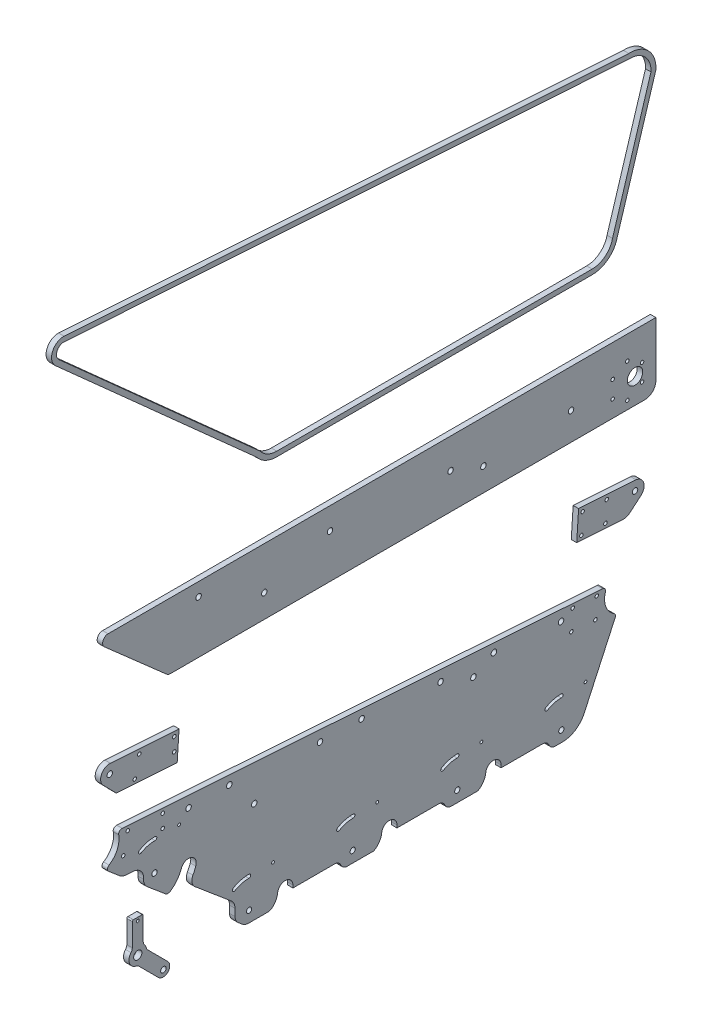
SolidWorks part; units mm, degrees
ref_plane "前视基准面" through (0, 0, 0) normal (0, 0, 1) x (1, 0, 0)
ref_plane "上视基准面" through (0, 0, 0) normal (0, 1, 0) x (1, 0, 0)
ref_plane "右视基准面" through (0, 0, 0) normal (1, 0, 0) x (0, 0, -1)
sketch "草图1" plane through (0, 0, 0) normal (1, 0, 0) x (0, 0, -1)
  line L14 (-230.0465, 110.9643) -> (-222.0465, 110.9643)
  line L15 (-216.9793, 80.6181) -> (-198.5946, 62.2334)
  line L16 (-221.0465, 89.2709) -> (-221.0465, 109.9643)
  line L17 (-231.0465, 89.2709) -> (-231.0465, 109.9643)
  line L18 (-225.09, 71.7583) -> (-207.0798, 53.7481)
  line L19 (105.5834, 65.6055) -> (105.5834, 63.2056)
  line L20 (10.5834, 65.6055) -> (10.5834, 63.181)
  line L21 (-236.8297, 149.6899) -> (-229.9878, 149.2348)
  line L22 (-84.4166, 65.6055) -> (-84.4166, 63.2014)
  line L23 (-137.2631, 67.0436) -> (-137.2631, 73.5793)
  line L24 (-252.6112, 160.4369) -> (-242.6047, 152.0164)
  line L25 (-200.3246, 116.3858) -> (-217.1392, 130.5351)
  line L26 (-173.8485, 109.0202) -> (-140.8245, 81.2308)
  line L27 (105.5834, 63.2056) -> (143.6903, 63.2056)
  line L28 (10.5834, 63.181) -> (48.7171, 63.181)
  line L29 (-84.4166, 63.2014) -> (-46.2562, 63.2014)
  line L30 (154.9968, 55.6055) -> (161.4882, 55.6055)
  line L31 (60.0128, 55.6055) -> (84.3359, 55.6055)
  line L32 (-34.8893, 55.6055) -> (-10.6641, 55.6055)
  line L33 (-240.2719, 188.3412) -> (198.1907, 158.5594)
  line L34 (181.4745, 68.4105) -> (209.7419, 129.8528)
  line L35 (-130.8865, 57.9541) -> (-134.414, 60.9224)
  line L36 (-124.4479, 55.6055) -> (-107.3213, 55.6055)
  line L37 (-190.0505, 215.1099) -> (-188.328, 241.0072)
  line L38 (-188.328, 241.0072) -> (-251.0362, 245.1782)
  line L39 (-245.6413, 218.8075) -> (-257.5624, 231.0237)
  line L40 (-245.6413, 218.8075) -> (-190.0505, 215.1099)
  line L47 (174.6512, 206.6476) -> (216.2373, 203.8816)
  line L48 (223.3686, 206.2326) -> (233.4205, 214.7564)
  line L49 (176.39, 232.7899) -> (174.6512, 206.6476)
  line L50 (176.39, 232.7899) -> (228.7265, 229.3088)
  line L122 (-293.5152, 599.4283) -> (222.2511, 565.1227)
  line L131 (242.4299, 544.9439) -> (207.3442, 430.9372)
  line L133 (188.77, 415.937) -> (-99.1762, 415.937)
  line L150 (-114.4994, 423.7032) -> (-297.9902, 587.7064)
  line L160 (246.8783, 348.5788) -> (246.8783, 298.5788)
  line L161 (246.8783, 348.5788) -> (-253.1217, 348.5788)
  line L162 (-256.4251, 339.8255) -> (-199.8991, 290.0748)
  line L164 (236.8783, 288.5788) -> (-195.935, 288.5788)
  line L166 (-293.3467, 603.927) -> (222.2719, 569.6313)
  line L167 (246.8783, 544.0995) -> (211.6993, 429.7897)
  line L168 (188.77, 411.437) -> (-99.1762, 411.437)
  line L169 (-117.831, 420.6454) -> (-300.9891, 584.3512)
  circle A0 centre (-228.79, 221.5342) radius 1.6
  arc A1 (-251.0362, 245.1782) -> (-257.5624, 231.0237) centre (-251.59, 236.8518) ccw
  circle A2 centre (-224.6325, 239.25) radius 1.6
  circle A3 centre (-251.59, 236.8518) radius 2.5
  circle A4 centre (-170.5361, 336.4269) radius 2.5
  circle A5 centre (89.4639, 309.8122) radius 2.5
  circle A6 centre (-192.7061, 237.0812) radius 1.6
  circle A7 centre (59.4639, 321.1287) radius 2.5
  circle A8 centre (-192.79, 225.0815) radius 1.6
  circle A11 centre (-110.5361, 309.8122) radius 2.5
  circle A12 centre (227.8783, 311.5857) radius 7
  circle A13 centre (169.4639, 313.8122) radius 2.5
  circle A14 centre (-50.5361, 328.4452) radius 2.5
  arc A15 (246.8783, 298.5788) -> (236.8783, 288.5788) centre (236.8783, 298.5788) cw
  circle A28 centre (234.3017, 319.3357) radius 1.6
  circle A29 centre (220.8783, 327.0857) radius 1.6
  circle A30 centre (207.4549, 319.3357) radius 1.6
  circle A31 centre (207.4549, 303.8357) radius 1.6
  circle A32 centre (220.8783, 296.0857) radius 1.6
  circle A33 centre (234.3017, 303.8357) radius 1.6
  arc A59 (-232.2003, 86.0761) -> (-227.6336, 73.1233) centre (-226.0465, 80.9643) ccw
  arc A60 (-218.291, 82.927) -> (-219.8926, 86.0761) centre (-226.0465, 80.9643) ccw
  arc A61 (-198.5946, 62.2334) -> (-207.0798, 53.7481) centre (-202.8372, 57.9907) cw
  circle A62 centre (-226.0465, 80.9643) radius 3.75
  arc A63 (-225.09, 71.7583) -> (-227.6336, 73.1233) centre (-228.6255, 68.2227) ccw
  arc A64 (-231.0465, 89.2709) -> (-232.2003, 86.0761) centre (-236.0465, 89.2709) cw
  arc A65 (-216.9793, 80.6181) -> (-218.291, 82.927) centre (-213.4438, 84.1537) cw
  arc A66 (-221.0465, 89.2709) -> (-219.8926, 86.0761) centre (-216.0465, 89.2709) ccw
  arc A67 (-221.0465, 109.9643) -> (-222.0465, 110.9643) centre (-222.0465, 109.9643) ccw
  arc A68 (-231.0465, 109.9643) -> (-230.0465, 110.9643) centre (-230.0465, 109.9643) cw
  circle A69 centre (-226.0465, 107.9643) radius 1.3
  circle A70 centre (-202.5944, 57.7479) radius 2.5
  circle A71 centre (160.3391, 151.5407) radius 2.5
  circle A72 centre (-179.6609, 174.1553) radius 2.5
  circle A73 centre (192.9424, 155.3853) radius 1.6
  circle A74 centre (50.3391, 158.8572) radius 2.5
  arc A75 (-130.8865, 57.9541) -> (-124.4479, 55.6055) centre (-124.4479, 65.6055) ccw
  arc A76 (161.4882, 55.6055) -> (181.4745, 68.4105) centre (161.4882, 77.6055) ccw
  circle A77 centre (80.3391, 147.5407) radius 2.5
  arc A78 (-40.9159, 59.9364) -> (-39.59, 57.8768) centre (-29.8465, 65.6055) ccw
  circle A79 centre (-119.6609, 147.5407) radius 2.5
  circle A80 centre (170.9909, 156.8454) radius 1.6
  circle A81 centre (-59.6609, 166.1737) radius 2.5
  arc A82 (54.0884, 59.8547) -> (55.122, 58.1299) centre (65.6415, 65.6055) ccw
  arc A83 (149.0664, 59.8697) -> (150.1013, 58.1364) centre (160.6415, 65.6055) ccw
  arc A84 (149.0664, 59.8697) -> (143.6903, 63.2056) centre (143.6903, 57.2056) ccw
  arc A85 (48.7171, 63.181) -> (54.0884, 59.8547) centre (48.7171, 57.181) cw
  arc A86 (-46.2562, 63.2014) -> (-40.9159, 59.9364) centre (-46.2562, 57.2014) cw
  circle A87 centre (169.783, 138.6855) radius 1.6
  circle A88 centre (191.7345, 137.2255) radius 1.6
  circle A89 centre (-235.1682, 183.9052) radius 1.6
  circle A90 centre (-203.2418, 181.7363) radius 1.6
  circle A91 centre (-239.3257, 166.1893) radius 1.6
  arc A92 (-103.7076, 56.8158) -> (-107.3213, 55.6055) centre (-107.3213, 61.6055) cw
  arc A93 (60.0128, 55.6055) -> (55.122, 58.1299) centre (60.0128, 61.6055) cw
  circle A94 centre (-188.2832, 165.2455) radius 1.3
  arc A95 (-34.8893, 55.6055) -> (-39.59, 57.8768) centre (-34.8893, 61.6055) cw
  arc A96 (-179.6609, 127.2391) -> (-193.1471, 110.3459) centre (-210.7713, 138.2455) cw construction
  arc A97 (-173.8485, 109.0202) -> (-175.7099, 118.992) centre (-168.6976, 115.1413) cw
  arc A98 (-196.8856, 116.264) -> (-200.3246, 116.3858) centre (-198.4616, 120.3771) cw
  arc A99 (-196.8856, 116.264) -> (-186.2601, 129.5738) centre (-210.7713, 138.2455) ccw
  arc A100 (154.9968, 55.6055) -> (150.1013, 58.1364) centre (154.9968, 61.6055) cw
  arc A101 (-140.8245, 81.2308) -> (-137.2631, 73.5793) centre (-147.2631, 73.5793) cw
  arc A102 (-236.8297, 149.6899) -> (-242.6047, 152.0164) centre (-236.1661, 159.6678) cw
  arc A103 (-229.9878, 149.2348) -> (-220.7032, 138.241) centre (-230.6515, 139.2569) cw
  arc A104 (-220.7032, 138.241) -> (-217.1392, 130.5351) centre (-211.8741, 137.6474) ccw
  arc A105 (-137.2631, 67.0436) -> (-134.414, 60.9224) centre (-129.2631, 67.0436) ccw
  arc A106 (-173.0617, 124.9044) -> (-186.2601, 129.5738) centre (-179.6609, 127.2391) ccw
  arc A107 (-175.7099, 118.992) -> (-173.0617, 124.9044) centre (-210.7713, 138.2455) ccw
  arc A108 (209.7419, 129.8528) -> (208.6362, 133.6318) centre (207.0165, 131.1066) ccw
  arc A109 (198.1907, 158.5594) -> (200.8593, 154.6992) centre (197.9874, 155.5663) cw
  arc A110 (-252.6112, 160.4369) -> (-252.2413, 165.2938) centre (-250.6796, 162.7323) cw
  arc A111 (-240.2719, 188.3412) -> (-243.4291, 184.8241) centre (-240.4752, 185.3481) ccw
  arc A112 (-210.2832, 165.2455) -> (-223.8045, 161.6159) centre (-210.7713, 140.0637) ccw construction
  arc A113 (-210.2522, 166.8452) -> (-224.6325, 162.985) centre (-210.7713, 140.0637) ccw
  arc A114 (-210.3142, 163.6458) -> (-222.9766, 160.2468) centre (-210.7713, 140.0637) ccw
  arc A115 (-210.3142, 163.6458) -> (-210.2522, 166.8452) centre (-210.2832, 165.2455) ccw
  arc A116 (-224.6325, 162.985) -> (-222.9766, 160.2468) centre (-223.8045, 161.6159) ccw
  circle A117 centre (-203.3257, 169.7366) radius 1.6
  circle A118 centre (-210.7713, 138.2455) radius 2.4
  circle A119 centre (-102.5698, 92.6055) radius 1.3
  arc A120 (-100.2131, 60.9055) -> (-103.7076, 56.8158) centre (-111.2189, 66.7716) cw
  circle A121 centre (87.6415, 92.6055) radius 1.3
  circle A122 centre (65.6415, 65.6055) radius 2.4
  arc A123 (89.7869, 60.9055) -> (91.5834, 65.6055) centre (79.7252, 67.4448) ccw
  circle A124 centre (-21.7236, 165.6547) radius 2.5
  arc A125 (-84.4166, 65.6055) -> (-98.4166, 65.6055) centre (-91.4166, 65.6055) ccw
  arc A126 (-5.2131, 60.9055) -> (-3.4166, 65.6055) centre (-15.2748, 67.4448) ccw
  circle A127 centre (-29.8465, 65.6055) radius 2.4
  circle A128 centre (-7.3585, 92.6055) radius 1.3
  arc A129 (-5.2131, 60.9055) -> (-10.6641, 55.6055) centre (-16.2189, 66.7716) cw
  circle A130 centre (-142.4886, 173.6873) radius 2.5
  circle A131 centre (99.0415, 157.6222) radius 2.5
  arc A134 (89.7869, 60.9055) -> (84.3359, 55.6055) centre (78.7811, 66.7716) cw
  arc A135 (105.5834, 65.6055) -> (91.5834, 65.6055) centre (98.5834, 65.6055) ccw
  arc A136 (-100.2131, 60.9055) -> (-98.4166, 65.6055) centre (-110.2748, 67.4448) ccw
  circle A137 centre (182.6415, 92.6055) radius 1.3
  arc A139 (-91.4166, 65.6055) -> (-95.4814, 55.6055) centre (-110.2748, 67.4448) cw construction
  circle A142 centre (-124.4166, 65.6055) radius 2.4
  arc A143 (-252.2413, 165.2938) -> (-243.4291, 184.8241) centre (-262.1257, 181.5069) ccw
  circle A145 centre (160.6415, 65.6055) radius 2.4
  arc A146 (200.8593, 154.6992) -> (208.6362, 133.6318) centre (218.6954, 149.3142) ccw
  arc A147 (10.5834, 65.6055) -> (-3.4166, 65.6055) centre (3.5834, 65.6055) ccw
  arc A148 (-29.3585, 92.6055) -> (-42.8798, 88.9759) centre (-29.8465, 67.4237) ccw construction
  arc A149 (-29.3275, 94.2052) -> (-43.7077, 90.345) centre (-29.8465, 67.4237) ccw
  arc A151 (-29.3895, 91.0058) -> (-42.0518, 87.6068) centre (-29.8465, 67.4237) ccw
  arc A152 (-29.3895, 91.0058) -> (-29.3275, 94.2052) centre (-29.3585, 92.6055) ccw
  arc A153 (-43.7077, 90.345) -> (-42.0518, 87.6068) centre (-42.8798, 88.9759) ccw
  arc A154 (-124.5698, 92.6055) -> (-138.0911, 88.9759) centre (-125.0579, 67.4237) ccw construction
  arc A155 (-124.5388, 94.2052) -> (-138.919, 90.345) centre (-125.0579, 67.4237) ccw
  arc A158 (-124.6008, 91.0058) -> (-137.2631, 87.6068) centre (-125.0579, 67.4237) ccw
  arc A159 (-124.6008, 91.0058) -> (-124.5388, 94.2052) centre (-124.5698, 92.6055) ccw
  arc A160 (-138.919, 90.345) -> (-137.2631, 87.6068) centre (-138.0911, 88.9759) ccw
  arc A161 (65.6415, 92.6055) -> (52.1202, 88.9759) centre (65.1535, 67.4237) ccw construction
  arc A163 (65.6725, 94.2052) -> (51.2923, 90.345) centre (65.1535, 67.4237) ccw
  arc A164 (65.6105, 91.0058) -> (52.9482, 87.6068) centre (65.1535, 67.4237) ccw
  arc A165 (65.6105, 91.0058) -> (65.6725, 94.2052) centre (65.6415, 92.6055) ccw
  circle A166 centre (180.1157, 228.5332) radius 1.6
  arc A169 (233.4205, 214.7564) -> (228.7265, 229.3088) centre (227.8783, 221.002) ccw
  circle A170 centre (200.8593, 208.9133) radius 1.6
  circle A171 centre (202.0672, 227.0732) radius 1.6
  circle A172 centre (227.8783, 221.002) radius 2.5
  circle A175 centre (178.9078, 210.3734) radius 1.6
  arc A176 (216.2373, 203.8816) -> (223.3686, 206.2326) centre (216.901, 213.8595) ccw
  arc A177 (51.2923, 90.345) -> (52.9482, 87.6068) centre (52.1202, 88.9759) ccw
  arc A178 (160.6415, 92.6055) -> (147.1202, 88.9759) centre (160.1535, 67.4237) ccw construction
  arc A180 (160.6725, 94.2052) -> (146.2923, 90.345) centre (160.1535, 67.4237) ccw
  arc A181 (160.6105, 91.0058) -> (147.9482, 87.6068) centre (160.1535, 67.4237) ccw
  arc A182 (160.6105, 91.0058) -> (160.6725, 94.2052) centre (160.6415, 92.6055) ccw
  arc A183 (146.2923, 90.345) -> (147.9482, 87.6068) centre (147.1202, 88.9759) ccw
  arc A481 (188.77, 415.937) -> (207.3442, 430.9372) centre (188.77, 434.937) ccw
  arc A521 (-199.8991, 290.0748) -> (-195.935, 288.5788) centre (-195.935, 294.5788) ccw
  arc A525 (-253.1217, 348.5788) -> (-256.4251, 339.8255) centre (-253.1217, 343.5788) ccw
  arc A526 (-293.5152, 599.4283) -> (-297.9902, 587.7064) centre (-293.5152, 592.7131) ccw
  arc A527 (-114.4994, 423.7032) -> (-99.1762, 415.937) centre (-99.1762, 434.937) ccw
  arc A528 (222.2511, 565.1227) -> (242.4299, 544.9439) centre (223.469, 546.1618) cw
  arc A529 (222.2719, 569.6313) -> (246.8783, 544.0995) centre (223.469, 546.1618) cw
  arc A530 (188.77, 411.437) -> (211.6993, 429.7897) centre (188.77, 434.937) ccw
  arc A531 (-117.831, 420.6454) -> (-99.1762, 411.437) centre (-99.1762, 434.937) ccw
  arc A532 (-293.3467, 603.927) -> (-300.9891, 584.3512) centre (-293.5152, 592.7131) ccw
  point P0 (-150, 0)
  point P1 (135, 0)
  point P9 (-344.9533, 138.7825)
  point P10 (187.1329, 101.1747)
  point P11 (165.9429, -19)
  point P12 (-156.9154, -19)
  point P90 (-202.4626, 49.1308)
  point P124 (-202.4626, 49.1308)
  point P152 (-202.4626, 49.1308)
  point P228 (-184.9816, 117.657)
  point P233 (-185.9751, 118.108)
  point P251 (-240.0956, 149.8528)
  point P269 (-217.3011, 164.3891)
  point P326 (-6.0834, 60.4072)
  point P400 (94.2902, 60.3053)
  point P405 (-106.0844, 60.4084)
  point P417 (-36.3764, 91.7491)
  point P427 (-131.5877, 91.7491)
  point P437 (58.6236, 91.7491)
  point P449 (153.6236, 91.7491)
  dimension "D7" = 8
  dimension "D8" = 10
  dimension "D9" = 10
  dimension "D10" = 10
  dimension "D4" = 6
  dimension "D11" = 10
  dimension "D12" = 27
  dimension "D13" = 10
  dimension "D14" = 27
  dimension "D15" = 27
  dimension "D16" = 27
  dimension "D17" = 7
  dimension "D18" = 7
  dimension "D19" = 8
  dimension "D20" = 10
  dimension "D6" = 10
  dimension "D5" = 6
  dimension "D21" = 3
  dimension "D22" = 4.8
  dimension "D2" = 22
  dimension "D1" = 10
  dimension "D3" = 6
extrude "凸台-拉伸2" add sketch "草图1" along normal blind 5
